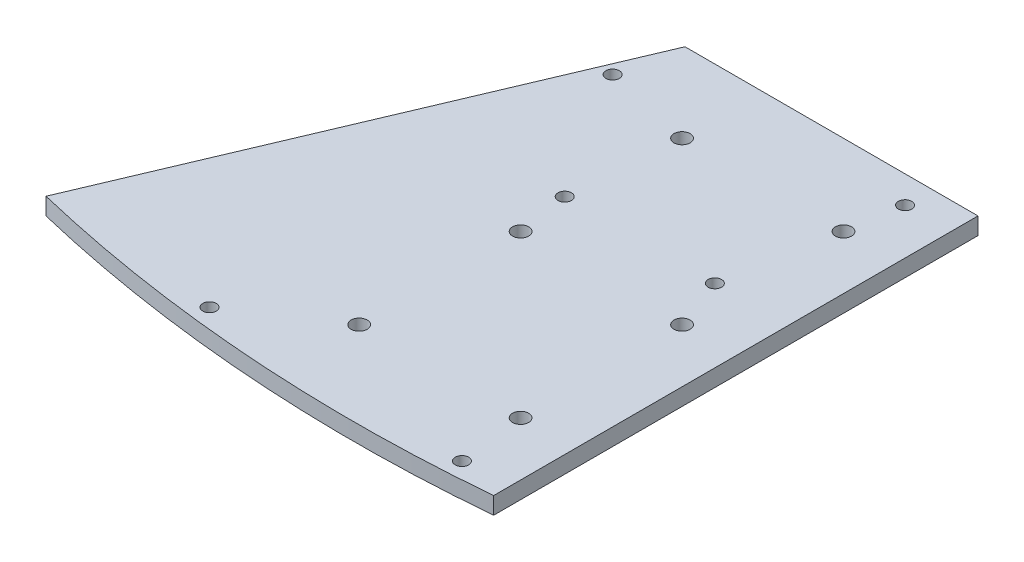
SolidWorks part; units mm, degrees
ref_plane "Front Plane" through (0, 0, 0) normal (0, 0, 1) x (1, 0, 0)
ref_plane "Top Plane" through (0, 0, 0) normal (0, 1, 0) x (1, 0, 0)
ref_plane "Right Plane" through (0, 0, 0) normal (1, 0, 0) x (0, 0, -1)
sketch "Sketch1" plane through (0, 0, 0) normal (0, 1, 0) x (1, 0, 0)
  line L0 (-30, 60) -> (-30, 0) construction
  line L1 (0, 60) -> (0, 0) construction
  line L2 (-46.7, -11.1) -> (1.5, -11.1) construction
  line L3 (-79.769, -8.4306) -> (-44.45, 75) construction
  line L4 (-44.45, 75) -> (10, 75)
  line L5 (10, 75) -> (10, -15)
  line L6 (0, 0) -> (-76.2, 0) construction
  line L7 (0, 60) -> (-50.8, 60) construction
  line L8 (1.5, -11.1) -> (1.5, -12.4) construction
  line L9 (-46.7, 63.8) -> (-46.7, -11.1) construction
  line L10 (1.5, 69.95) -> (1.5, -12.4) construction
  line L11 (-31.5, 39.7) -> (-3.6, 39.7) construction
  line L12 (-44.45, 75) -> (-79.769, -8.4306)
  line L14 (-49.2, 76.5) -> (4, 76.5) construction
  line L15 (-49.2, 76.5) -> (-49.2, -25.1) construction
  line L16 (-49.2, -25.1) -> (4, -25.1) construction
  line L17 (4, 76.5) -> (4, -25.1) construction
  circle A0 centre (0, 0) radius 1.5
  circle A1 centre (-30, 0) radius 1.5
  circle A2 centre (-30, 30) radius 1.5
  circle A3 centre (-30, 60) radius 1.5
  circle A4 centre (0, 60) radius 1.5
  circle A5 centre (0, 30) radius 1.5
  circle A6 centre (-46.7, 63.8) radius 1.25
  circle A7 centre (1.5, 69.95) radius 1.25
  circle A8 centre (-31.5, 39.7) radius 1.25
  circle A9 centre (-3.6, 39.7) radius 1.25
  circle A10 centre (-46.7, -11.1) radius 1.25
  arc A11 (-79.769, -8.4306) -> (10, -15) centre (-15, 260) ccw
  circle A12 centre (1.5, -12.4) radius 1.25
  dimension "D1" = 3
  dimension "D2" = 30
  dimension "D9" = 15
  dimension "D7" = 2.5
  dimension "D3" = 60
  dimension "D4" = 60
  dimension "D5" = 76.2
  dimension "D6" = 10
  dimension "D8" = 50.8
  dimension "D10" = 48.2
  dimension "D11" = 1.3
  dimension "D12" = 82.35
  dimension "D13" = 74.9
  dimension "D14" = 50.8
  dimension "D15" = 15.2
  dimension "D16" = 27.9
  dimension "D17" = 14
  dimension "D18" = 101.6
  dimension "D19" = 2.5
  dimension "D20" = 2.5
  dimension "D21" = 3
  dimension "D22" = 6
extrude "Boss-Extrude1" add sketch "Sketch1" along normal blind 3.175
